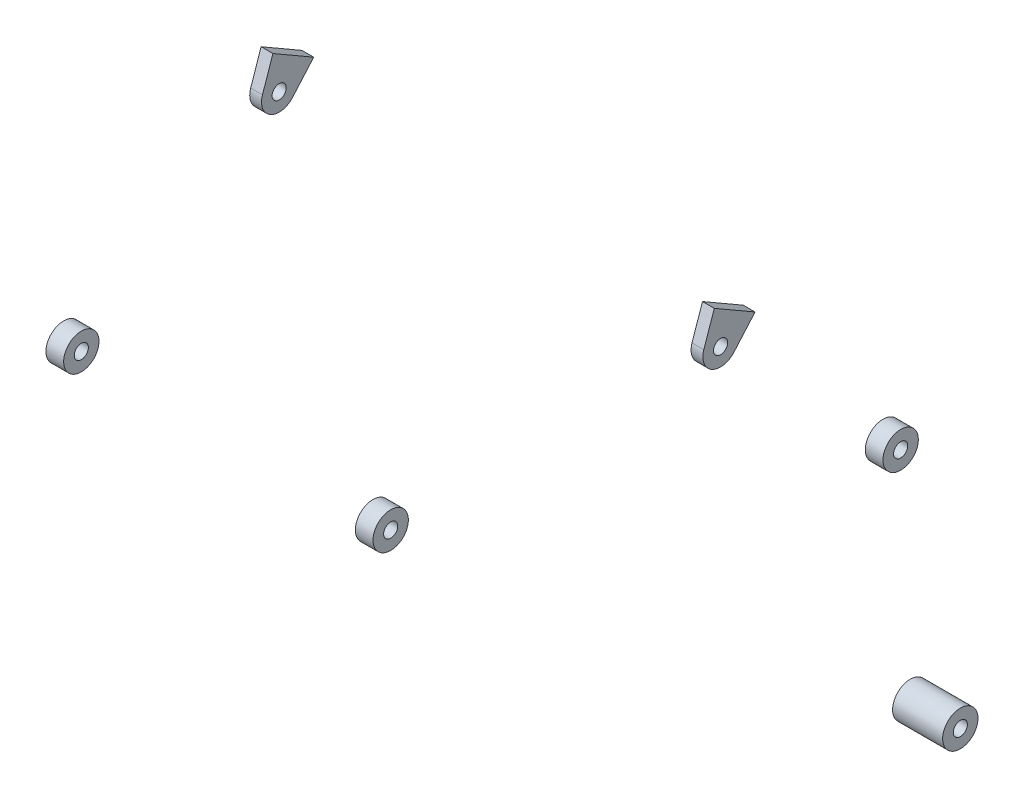
SolidWorks part; units mm, degrees
ref_plane "Front" through (0, 0, 0) normal (0, 0, 1) x (1, 0, 0)
ref_plane "Top" through (0, 0, 0) normal (0, 1, 0) x (1, 0, 0)
ref_plane "Right" through (0, 0, 0) normal (1, 0, 0) x (0, 0, -1)
sketch "Sketch1" plane through (0, 0, 0) normal (1, 0, 0) x (0, 0, -1)
  line L0 (0, 0) -> (-226.3851, -48.3945) construction
  dimension "D1" = 231.5
sketch "Sketch2" plane through (0, 0, 0) normal (1, 0, 0) x (0, 0, -1)
  line L0 (-5.3205, 30.7846) -> (29.3205, 10.7846)
  line L1 (-14.1922, 4.856) -> (-5.3205, 30.7846)
  line L3 (11.3015, -9.8628) -> (29.3205, 10.7846)
  line L4 (0, 0) -> (53.6021, 0) construction
  circle A0 centre (0, 0) radius 6
  arc A1 (-14.1922, 4.856) -> (11.3015, -9.8628) centre (0, 0) ccw
  dimension "D2" = 30
  dimension "D3" = 12
  dimension "D1" = 150
  dimension "D4" = 40
  dimension "D5" = 24
extrude "Boss-Extrude1" add sketch "Sketch2" along normal blind 10
ref_plane "Plane1" through (-43.5, 0, 0) normal (1, 0, 0) x (0, 0, -1)
sketch "Sketch3" plane through (-43.5, 0, 0) normal (1, 0, 0) x (0, 0, -1)
  circle A0 centre (-226.3851, -48.3945) radius 6
  circle A1 centre (-226.3851, -48.3945) radius 15
  dimension "D1" = 12
  dimension "D2" = 30
extrude "Boss-Extrude2" add sketch "Sketch3" against normal blind 15 separate body
sketch "Sketch4" plane through (-43.5, 0, 0) normal (1, 0, 0) x (0, 0, -1)
  line L0 (-226.3851, -48.3945) -> (243.4571, -422.3577) construction
  line L1 (0, 0) -> (-226.3851, -48.3945) construction
  dimension "D1" = 600.5
  dimension "D2" = 50.584
ref_plane "Plane2" through (-72.5, 0, 0) normal (1, 0, 0) x (0, 0, -1)
sketch "Sketch5" plane through (-72.5, 0, 0) normal (1, 0, 0) x (0, 0, -1)
  circle A0 centre (243.4571, -422.3577) radius 6
  circle A1 centre (243.4571, -422.3577) radius 15
  dimension "D1" = 12
  dimension "D2" = 30
extrude "Boss-Extrude3" add sketch "Sketch5" along normal blind 42.5 separate body
sketch "Sketch6" plane through (-30, 0, 0) normal (1, 0, 0) x (0, 0, -1)
  line L0 (243.4571, -422.3577) -> (0, 0) construction
ref_plane "Plane3" through (-51.5, 0, 0) normal (1, 0, 0) x (0, 0, -1)
sketch "Sketch7" plane through (-51.5, 0, 0) normal (1, 0, 0) x (0, 0, -1)
  line L0 (-226.3851, -48.3945) -> (199.3407, -198.76)
  line L1 (199.3407, -198.76) -> (0, 0)
  line L2 (199.3407, -198.76) -> (243.4571, -422.3577)
  circle A1 centre (199.3407, -198.76) radius 6
  circle A2 centre (199.3407, -198.76) radius 15
  point P3 (199.3407, -198.76)
  dimension "D3" = 12
  dimension "D4" = 30
  dimension "D1" = 451.5
  dimension "D2" = 281.5
extrude "Boss-Extrude4" add sketch "Sketch7" along normal blind 15 separate body contours L0 A2 L2 A1 | L2 A2 L1 A1 | L1 A2 L0 A1
ref_plane "Plane4" through (-182.25, 0, 0) normal (-1, 0, 0) x (0, 0, 1)
mirror "Mirror5" about plane through (-182.25, 0, 0) normal (-1, 0, 0) of bodies 102 101
